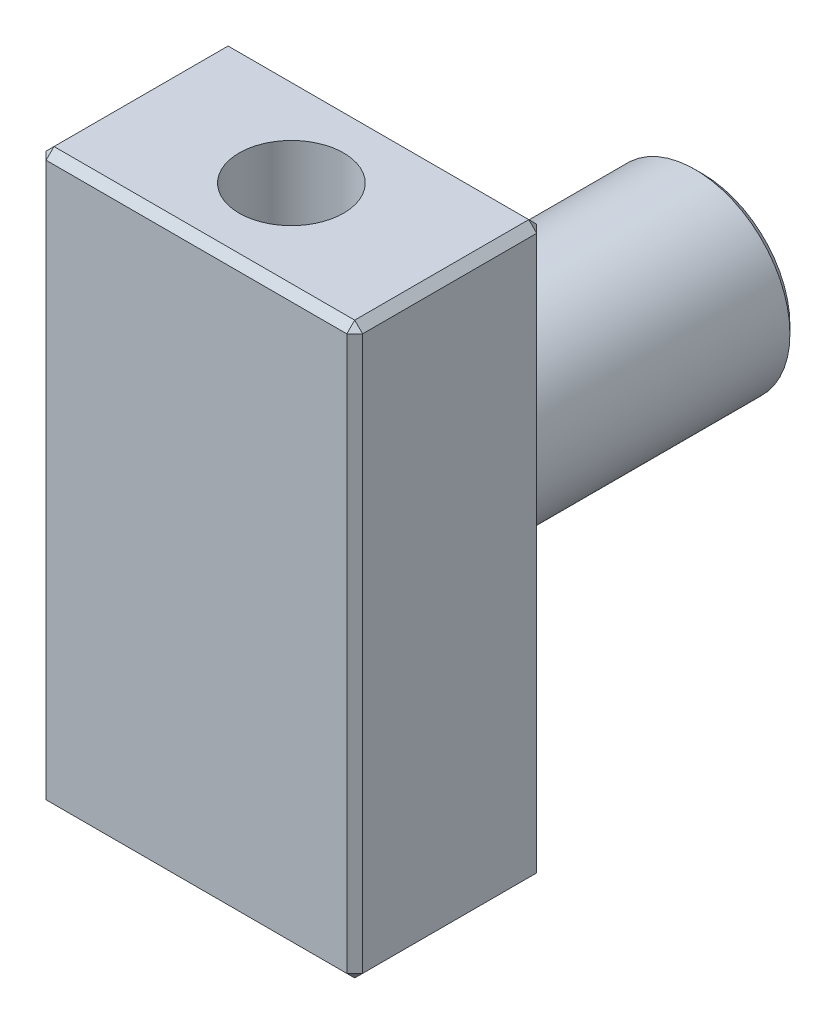
SolidWorks part; units mm, degrees
material "1060 Alloy"
ref_plane "Front Plane" through (0, 0, 0) normal (0, 0, 1) x (1, 0, 0)
ref_plane "Top Plane" through (0, 0, 0) normal (0, 1, 0) x (1, 0, 0)
ref_plane "Right Plane" through (0, 0, 0) normal (1, 0, 0) x (0, 0, -1)
sketch "Sketch1" plane through (0, 0, 0) normal (0, 0, 1) x (1, 0, 0)
  line L0 (-5, 9) -> (5, -9) construction
  line L1 (-5, 9) -> (5, 9)
  line L2 (-5, 9) -> (-5, -9)
  line L3 (-5, -9) -> (5, -9)
  line L4 (5, 9) -> (5, -9)
  point P4 (0, 0)
  dimension "D1" = 18
  dimension "D2" = 10
extrude "Extrude1" add sketch "Sketch1" along normal blind 6
sketch "Sketch2" plane through (0, 0, 0) normal (0, 0, -1) x (-1, 0, 0)
  circle A0 centre (0, 0) radius 3
  dimension "D1" = 6
extrude "Extrude2" add sketch "Sketch2" along normal blind 10
hole_wizard "M4x0.7 Tapped Hole1" positions "3DSketch1" profile "Sketch3" tap size "M4x0.7" standard "Ansi Metric"
sketch3d "3DSketch1"
  point P0 (0, -9, 3)
  point P2 (0, 9, 3)
  dimension "D1" = 5
  dimension "D2" = 3
sketch "Sketch3" plane through (0, -9, 3) normal (1, 0, 0) x (0, 0, -1)
  line L0 (0, 0) -> (0, 8.9914)
  line L1 (0, 8.9914) -> (1.65, 8)
  line L2 (1.65, 8) -> (1.65, 0)
  line L5 (1.65, 0) -> (0, 0)
  line L10 (0, 8.9914) -> (-1.65, 8) construction
  line L11 (0, -6.35) -> (0, 107.95) construction
  dimension "Tap Drill Dia." = 3.3
  dimension "Tap Drill Depth" = 8
  dimension "Drill Angle" = 118
cosmetic thread "Hole Thread1" parameters "D1"=8, "D2"=4
cosmetic thread "Hole Thread2" parameters "D1"=8, "D2"=4
chamfer "Chamfer3" distance 0.25 angle 45 14 edges at (3, 0, 0) (-5, 9, 3) (-5, -9, 3) (0, 9, 6) (-5, 0, 6) (0, -9, 6) (5, -9, 3) (5, 0, 6) (5, 9, 3) (0, -9, 0) (5, 0, 0) (0, 9, 0) (-5, 0, 0) (-3, 0, -10)
